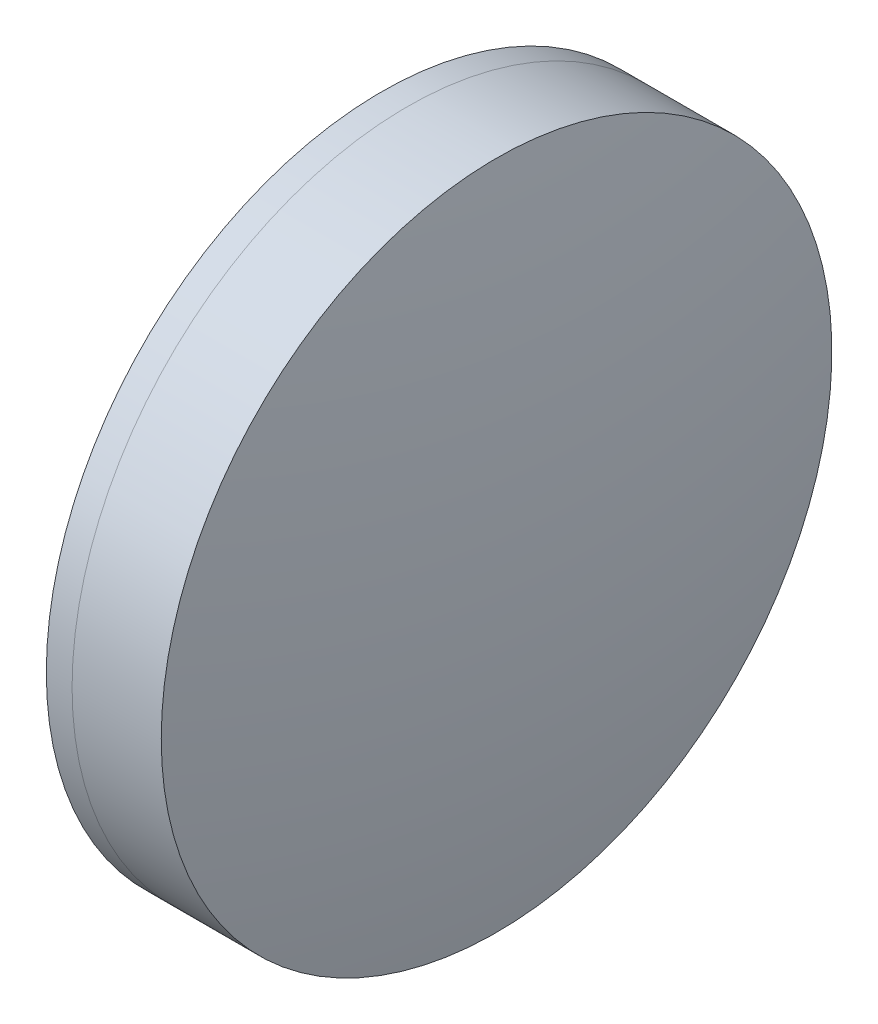
SolidWorks part; units mm, degrees
ref_plane "前视基准面" through (0, 0, 0) normal (0, 0, 1) x (1, 0, 0)
ref_plane "上视基准面" through (0, 0, 0) normal (0, 1, 0) x (1, 0, 0)
ref_plane "右视基准面" through (0, 0, 0) normal (1, 0, 0) x (0, 0, -1)
sketch "草图1" plane through (0, 0, 0) normal (0, 1, 0) x (1, 0, 0)
  line L0 (124.5233, 0) -> (395.1269, 0) construction
  line L1 (220.7739, -25) -> (222.6947, -25)
  line L2 (220.7739, 25) -> (222.6947, 25)
  arc A0 (222.6947, -25) -> (222.6947, 25) centre (181.4885, 0) ccw
  arc A1 (220.7739, 25) -> (220.7739, -25) centre (281.0555, 0) ccw
  point P10 (215.7955, 0)
  point P11 (229.6855, 0)
  dimension "D3" = 65.26
  dimension "D4" = 48.197
  dimension "D1" = 25
  dimension "D2" = 25
  dimension "D5" = 13.89
revolve "旋转1" add sketch "草图1" angle 360 about L0
sketch "草图2" plane through (0, 0, 0) normal (0, 1, 0) x (1, 0, 0)
  line L0 (-0.5519, 0) -> (409.4962, 0) construction
  line L2 (222.6947, 25) -> (229.3432, 25)
  line L3 (222.6947, -25) -> (229.3432, -25)
  arc A0 (229.3432, -25) -> (229.3432, 25) centre (97.0935, 0) ccw
  arc A1 (222.6947, -25) -> (222.6947, 25) centre (181.4885, 0) ccw construction
  arc A2 (222.6947, -25) -> (222.6947, 25) centre (181.4885, 0) ccw
  point P4 (229.6855, 0)
  point P8 (231.6855, 0)
  dimension "D1" = 134.592
  dimension "D2" = 2
revolve "旋转3" add sketch "草图2" angle 360 about L0
